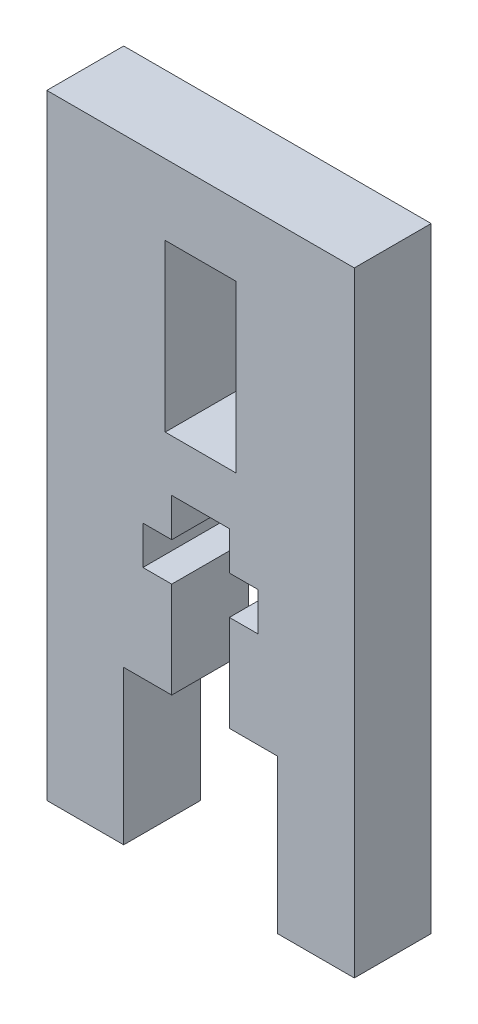
SolidWorks part; units mm, degrees
ref_plane "Front Plane" through (0, 0, 0) normal (0, 0, 1) x (1, 0, 0)
ref_plane "Top Plane" through (0, 0, 0) normal (0, 1, 0) x (1, 0, 0)
ref_plane "Right Plane" through (0, 0, 0) normal (1, 0, 0) x (0, 0, -1)
sketch "Sketch7" plane through (0, 0, 0) normal (0, 0, 1) x (1, 0, 0)
  line L0 (6.35, -25.4) -> (12.7, -25.4)
  line L1 (-12.7, -25.4) -> (-6.35, -25.4)
  line L2 (-12.7, -25.4) -> (-12.7, 25.4)
  line L3 (-12.7, 25.4) -> (12.7, 25.4)
  line L4 (12.7, -25.4) -> (12.7, 25.4)
  line L5 (-12.7, -25.4) -> (12.7, 25.4) construction
  line L6 (-12.7, 25.4) -> (12.7, -25.4) construction
  line L7 (-6.35, -12.7) -> (6.35, -12.7)
  line L8 (-6.35, -12.7) -> (-6.35, -25.4)
  line L10 (6.35, -12.7) -> (6.35, -25.4)
  line L11 (-6.35, -12.7) -> (6.35, -25.4) construction
  line L12 (-6.35, -25.4) -> (6.35, -12.7) construction
  point P0 (0, 0)
  point P6 (0, -19.05)
  dimension "D1" = 25.4
  dimension "D2" = 50.8
  dimension "D3" = 12.7
  dimension "D4" = 12.7
  dimension "D5" = 0
extrude "Boss-Extrude1" add sketch "Sketch7" along normal blind 6.35
sketch "Sketch8" plane through (0, 0, 6.35) normal (0, 0, 1) x (1, 0, 0)
  line L0 (-6.35, -12.7) -> (6.35, -12.7) construction
  line L1 (-2.3813, 1.5875) -> (2.3812, 1.5875)
  line L2 (-2.3813, 1.5875) -> (-2.3813, -12.7)
  line L3 (-2.3813, -12.7) -> (2.3813, -12.7)
  line L4 (2.3812, 1.5875) -> (2.3813, -12.7)
  line L5 (-2.3813, 1.5875) -> (2.3813, -12.7) construction
  line L6 (-2.3813, -12.7) -> (2.3812, 1.5875) construction
  line L8 (4.7625, -1.5875) -> (-4.7625, -1.5875)
  line L9 (4.7625, -1.5875) -> (4.7625, -4.7625)
  line L10 (4.7625, -4.7625) -> (-4.7625, -4.7625)
  line L11 (-4.7625, -1.5875) -> (-4.7625, -4.7625)
  line L12 (4.7625, -1.5875) -> (-4.7625, -4.7625) construction
  line L13 (4.7625, -4.7625) -> (-4.7625, -1.5875) construction
  point P0 (0, -5.5563)
  point P7 (0, -3.175)
  point P12 (0, -12.7)
  dimension "D1" = 14.2875
  dimension "D2" = 7.9375
  dimension "D3" = 3.175
  dimension "D4" = 4.7625
  dimension "D5" = 0
  dimension "D6" = 0
  dimension "D7" = 9.525
extrude "Cut-Extrude5" cut sketch "Sketch8" against normal blind 6.35 contours L8 L11 L10 L9 | L1 L4 L3 L2
sketch "Sketch9" plane through (0, 0, 6.35) normal (0, 0, 1) x (1, 0, 0)
  line L1 (-2.921, 19.558) -> (2.921, 19.558)
  line L2 (-2.921, 19.558) -> (-2.921, 5.842)
  line L3 (-2.921, 5.842) -> (2.921, 5.842)
  line L4 (2.921, 19.558) -> (2.921, 5.842)
  line L5 (-2.921, 19.558) -> (2.921, 5.842) construction
  line L6 (-2.921, 5.842) -> (2.921, 19.558) construction
  point P0 (0, 12.7)
  dimension "D1" = 5.842
  dimension "D2" = 13.716
  dimension "D3" = 0
  dimension "D4" = 12.7
extrude "Cut-Extrude6" cut sketch "Sketch9" against normal blind 6.35
